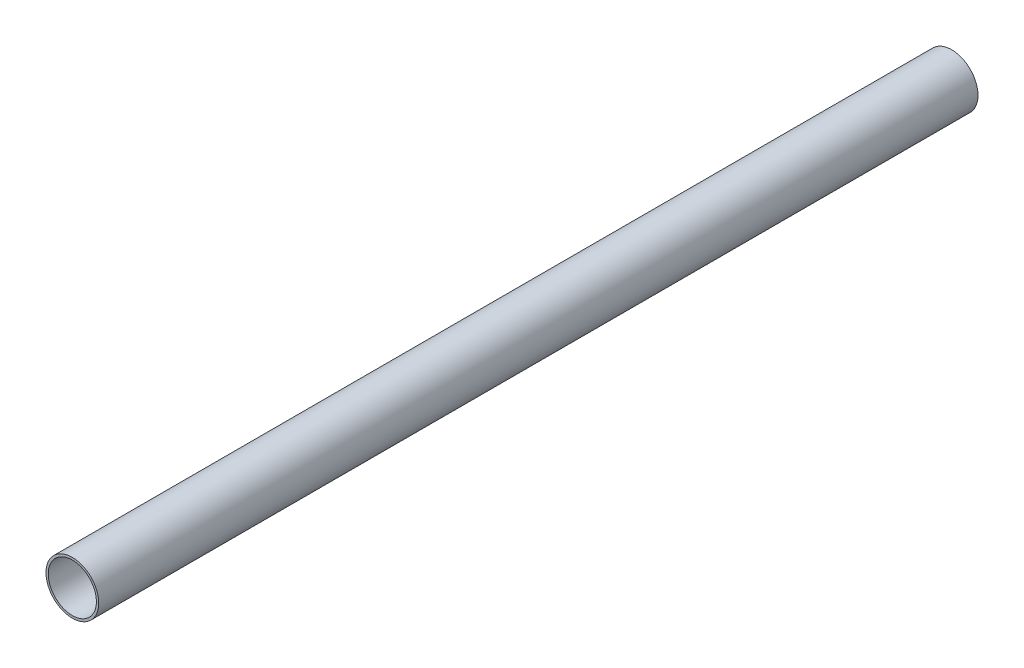
SolidWorks part; units mm, degrees
ref_plane "Plan de face" through (0, 0, 0) normal (0, 0, 1) x (1, 0, 0)
ref_plane "Plan de dessus" through (0, 0, 0) normal (0, 1, 0) x (1, 0, 0)
ref_plane "Plan de droite" through (0, 0, 0) normal (1, 0, 0) x (0, 0, -1)
sketch "Esquisse1" plane through (0, 0, 0) normal (0, 0, 1) x (1, 0, 0)
  circle A0 centre (0, 0) radius 12
  circle A1 centre (0, 0) radius 10.95
  dimension "D1" = 24
  dimension "D2" = 21.9
extrude "Boss.-Extru.1" add sketch "Esquisse1" along normal blind 400
